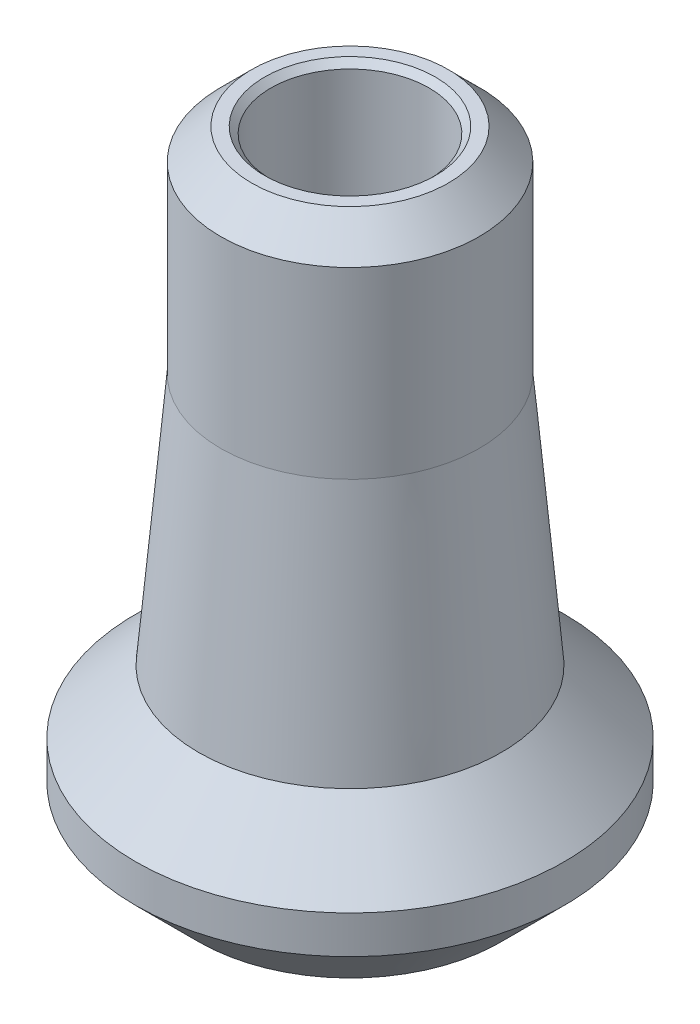
SolidWorks part; units mm, degrees
ref_plane "Front Plane" through (0, 0, 0) normal (0, 0, 1) x (1, 0, 0)
ref_plane "Top Plane" through (0, 0, 0) normal (0, 1, 0) x (1, 0, 0)
ref_plane "Right Plane" through (0, 0, 0) normal (1, 0, 0) x (0, 0, -1)
sketch "Sketch1" plane through (0, 0, 0) normal (0, 0, 1) x (1, 0, 0)
  line L0 (0, 0) -> (0, -60.6613) construction
  line L1 (-3.9624, 0) -> (-3.1877, 0)
  line L2 (-3.1877, 0) -> (-3.1877, -25.4)
  line L3 (-3.1877, -25.4) -> (-3.1877, 0)
  line L5 (-5.207, -8.6347) -> (-6.096, -18.796)
  line L6 (-6.096, -18.796) -> (-8.636, -21.336)
  line L7 (-8.636, -21.336) -> (-8.636, -22.86)
  line L8 (-3.9624, 0) -> (-5.207, -1.2446)
  line L9 (-8.636, -22.86) -> (-6.096, -25.4)
  line L10 (-6.096, -25.4) -> (-3.1877, -25.4)
  line L11 (-5.207, -1.2446) -> (-5.207, -8.6347)
other "AlignGroup1" parameters "D1"=3.9189, "D2"=5.099, "D3"=5.1165, "D4"=0, "D5"=8.128, "D6"=33.5246, "D7"=38.4544, "D8"=43.5709, "D9"=47.1782, "D10"=30.9224, "D11"=2.5438, "D12"=8.6688, "D13"=1.27, "D14"=6.858
revolve "Revolve1" add sketch "Sketch1" angle 360 about L0
chamfer "Chamfer1" distance 0.254 angle 45 2 edges at (0, 0, 3.1877) (0, -25.4, 3.1877)
